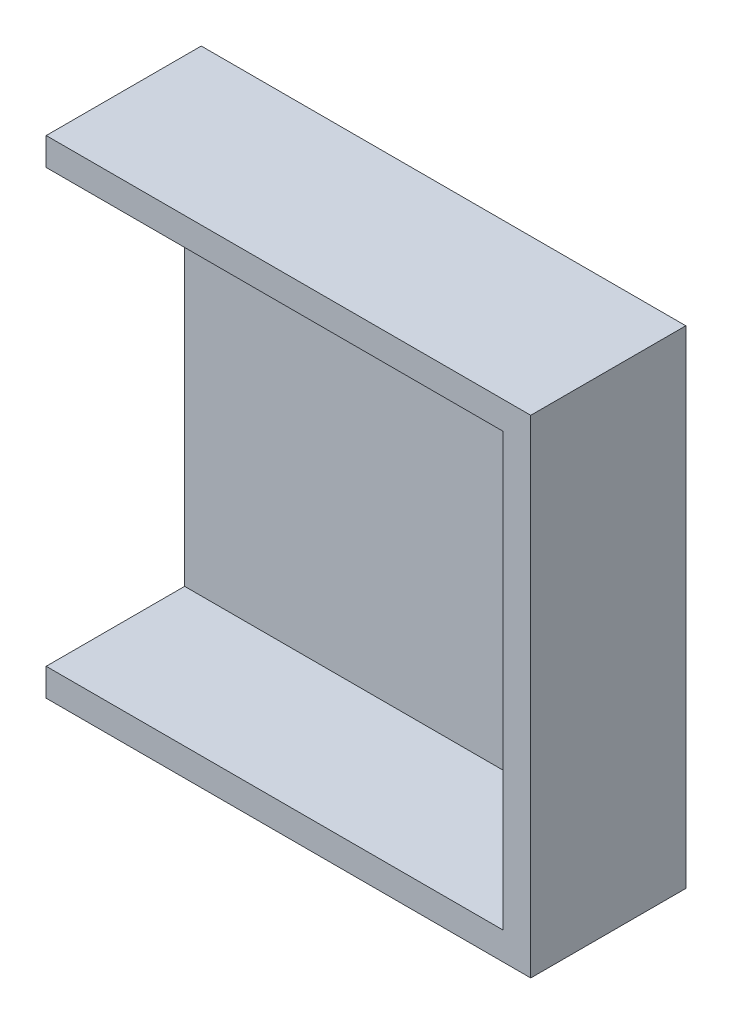
SolidWorks part; units mm, degrees
ref_plane "Alzado" through (0, 0, 0) normal (0, 0, 1) x (1, 0, 0)
ref_plane "Planta" through (0, 0, 0) normal (0, 1, 0) x (1, 0, 0)
ref_plane "Vista lateral" through (0, 0, 0) normal (1, 0, 0) x (0, 0, -1)
sketch "Croquis1" plane through (0, 0, 0) normal (0, 0, 1) x (1, 0, 0)
  line L1 (-63.5908, 16.5527) -> (-28.5908, 16.5527)
  line L2 (-63.5908, 16.5527) -> (-63.5908, -18.6473)
  line L3 (-63.5908, -18.6473) -> (-28.5908, -18.6473)
  line L4 (-28.5908, 16.5527) -> (-28.5908, -18.6473)
  dimension "D1" = 35.2
  dimension "D2" = 35
extrude "Saliente-Extruir1" add sketch "Croquis1" along normal blind 1.2
sketch "Croquis2" plane through (0, 0, 1.2) normal (0, 0, 1) x (1, 0, 0)
  line L0 (-63.5908, 16.5527) -> (-63.5908, 14.5527)
  line L1 (-63.5908, 16.5527) -> (-63.5908, -18.6473) construction
  line L2 (-63.5908, 14.5527) -> (-30.5908, 14.5527)
  line L3 (-30.5908, 14.5527) -> (-30.5908, -16.6473)
  line L4 (-30.5908, -16.6473) -> (-63.5908, -16.6473)
  line L5 (-63.5908, -16.6473) -> (-63.5908, -18.6473)
  line L6 (-63.5908, -18.6473) -> (-28.5908, -18.6473)
  line L7 (-28.5908, -18.6473) -> (-28.5908, 16.5527)
  line L8 (-28.5908, 16.5527) -> (-63.5908, 16.5527)
extrude "Saliente-Extruir2" add sketch "Croquis2" along normal blind 10
